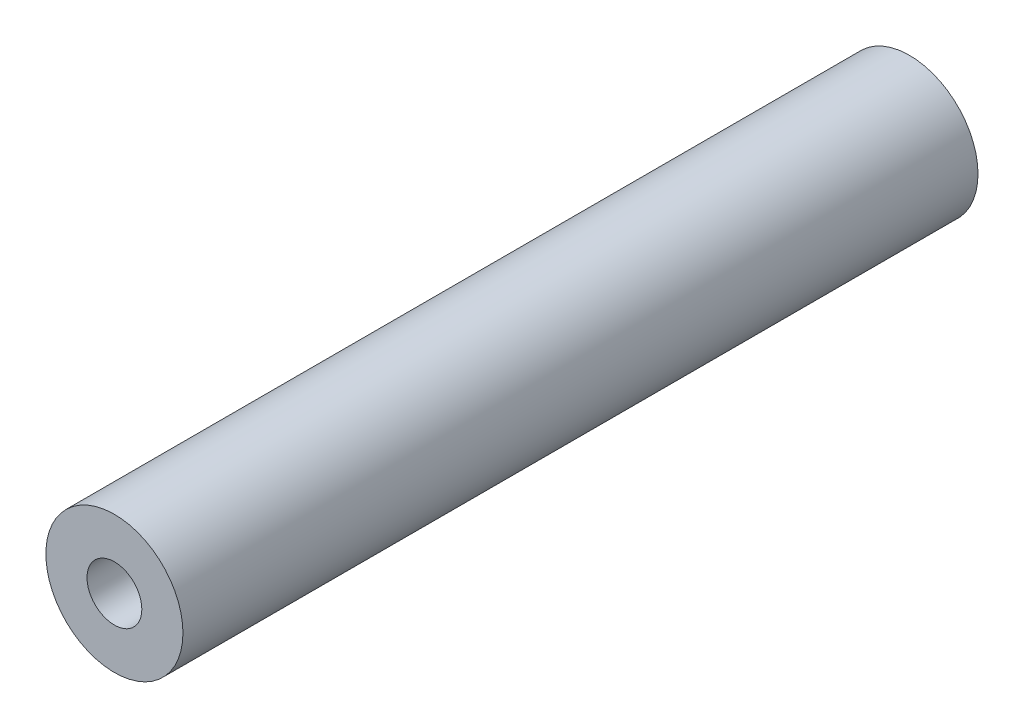
SolidWorks part; units mm, degrees
ref_plane "Front Plane" through (0, 0, 0) normal (0, 0, 1) x (1, 0, 0)
ref_plane "Top Plane" through (0, 0, 0) normal (0, 1, 0) x (1, 0, 0)
ref_plane "Right Plane" through (0, 0, 0) normal (1, 0, 0) x (0, 0, -1)
sketch "Sketch1" plane through (0, 0, 0) normal (0, 0, 1) x (1, 0, 0)
  circle A0 centre (4.6066, -4.4711) radius 5
  circle A1 centre (4.6066, -4.4711) radius 2
  dimension "D1" = 10
  dimension "D2" = 4
extrude "Boss-Extrude1" add sketch "Sketch1" along normal blind 58
